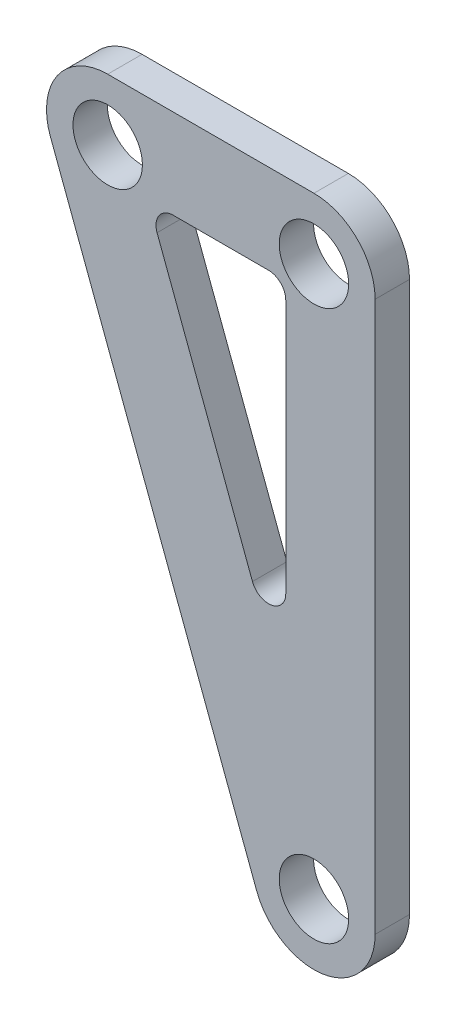
SolidWorks part; units mm, degrees
material "ABS"
ref_plane "Plan de face" through (0, 0, 0) normal (0, 0, 1) x (1, 0, 0)
ref_plane "Plan de dessus" through (0, 0, 0) normal (0, 1, 0) x (1, 0, 0)
ref_plane "Plan de droite" through (0, 0, 0) normal (1, 0, 0) x (0, 0, -1)
sketch "Esquisse1" plane through (0, 0, 0) normal (0, 0, 1) x (1, 0, 0)
  line L0 (-10.5833, -3.9687) -> (27.5167, -105.5687)
  line L1 (0, 11.303) -> (38.1, 11.303)
  line L2 (49.403, 0) -> (49.403, -101.6)
  line L3 (7.5137, -5.207) -> (32.893, -72.8851)
  line L4 (32.893, -5.207) -> (32.893, -72.8851)
  line L5 (7.5137, -5.207) -> (32.893, -5.207)
  arc A2 (0, 11.303) -> (-10.5833, -3.9687) centre (0, 0) ccw
  circle A3 centre (0, 0) radius 6.4135
  circle A6 centre (38.1, 0) radius 6.4135
  arc A7 (49.403, 0) -> (38.1, 11.303) centre (38.1, 0) ccw
  circle A8 centre (38.1, -101.6) radius 6.4135
  arc A9 (27.5167, -105.5687) -> (49.403, -101.6) centre (38.1, -101.6) ccw
  arc A10 (32.893, -72.8851) -> (32.893, -72.8851) centre (32.893, -72.8851) ccw
  arc A11 (32.893, -5.207) -> (32.893, -5.207) centre (32.893, -5.207) ccw
  arc A12 (7.5137, -5.207) -> (7.5137, -5.207) centre (7.5137, -5.207) ccw
  dimension "D1" = 12.827
  dimension "D2" = 11.303
  dimension "D3" = 101.6
  dimension "D4" = 38.1
  dimension "D5" = 16.51
extrude "Boss.-Extru.1" add sketch "Esquisse1" along normal blind 6.35
fillet "Congé1" radius 3.175 3 edges at (32.893, -72.8851, 3.175) (32.893, -5.207, 3.175) (7.5137, -5.207, 3.175)
